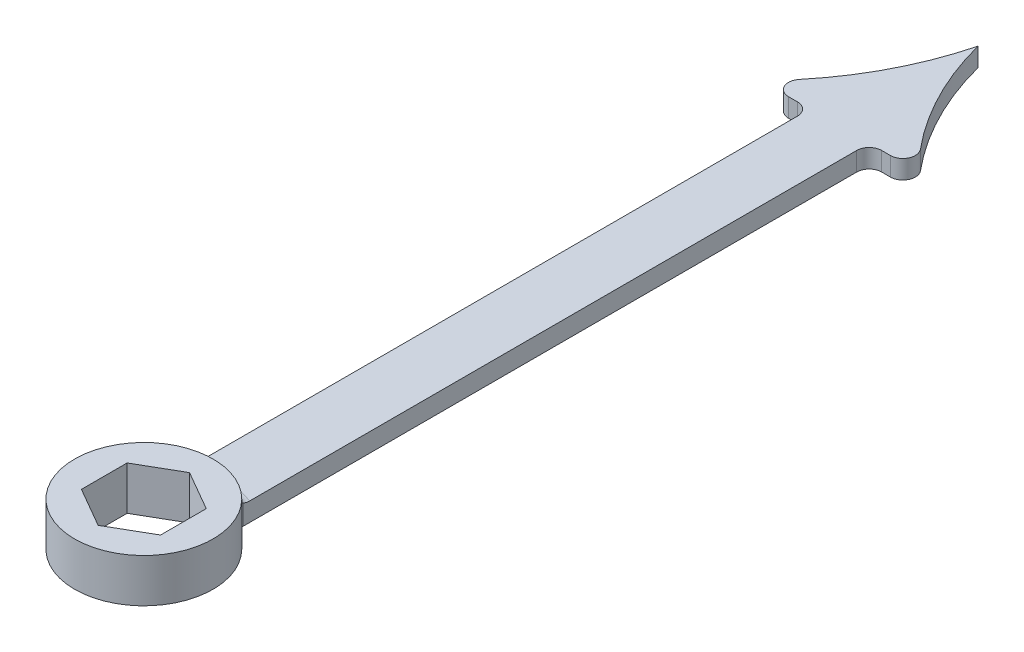
SolidWorks part; units mm, degrees
ref_plane "Front Plane" through (0, 0, 0) normal (0, 0, 1) x (1, 0, 0)
ref_plane "Top Plane" through (0, 0, 0) normal (0, 1, 0) x (1, 0, 0)
ref_plane "Right Plane" through (0, 0, 0) normal (1, 0, 0) x (0, 0, -1)
sketch "Sketch1" plane through (0, 0, 0) normal (0, 1, 0) x (1, 0, 0)
  line L1 (6.35, 3.6662) -> (0, 7.3323)
  line L2 (0, 7.3323) -> (-6.35, 3.6662)
  line L3 (-6.35, 3.6662) -> (-6.35, -3.6662)
  line L4 (-6.35, -3.6662) -> (0, -7.3323)
  line L5 (0, -7.3323) -> (6.35, -3.6662)
  line L6 (6.35, -3.6662) -> (6.35, 3.6662)
  circle A0 centre (0, 0) radius 6.35 construction
  circle A1 centre (0, 0) radius 11.1125
  dimension "D2" = 22.225
  dimension "D1" = 12.7
extrude "Boss-Extrude1" add sketch "Sketch1" along normal blind 7
sketch "Sketch2" plane through (0, 0, 0) normal (0, 1, 0) x (1, 0, 0)
  line L0 (-4.7625, 111.6402) -> (-12.7, 111.6402)
  line L1 (-4.7625, 111.6402) -> (4.7625, 111.6402) construction
  line L2 (-4.7625, 111.6402) -> (-4.7625, 10.0402)
  line L3 (-4.7625, 10.0402) -> (4.7625, 10.0402)
  line L4 (4.7625, 111.6402) -> (4.7625, 10.0402)
  line L5 (-12.7, 111.6402) -> (0, 124.3402) construction
  line L6 (0, 124.3402) -> (12.7, 111.6402) construction
  line L7 (12.7, 111.6402) -> (4.7625, 111.6402)
  line L8 (0, 133.8652) -> (0, 124.3402) construction
  circle A0 centre (0, 0) radius 11.1125 construction
  arc A1 (-12.7, 111.6402) -> (0, 133.8652) centre (-47.0958, 146.0361) ccw
  arc A2 (12.7, 111.6402) -> (0, 133.8652) centre (47.0958, 146.0361) cw
  point P11 (12.7, 111.6402)
  point P12 (0, 133.5515)
  dimension "D1" = 9.525
  dimension "D2" = 101.6
  dimension "D3" = 90
  dimension "D4" = 12.7
  dimension "D5" = 9.525
extrude "Boss-Extrude2" add sketch "Sketch2" along normal blind 3
fillet "Fillet1" radius 2 7 edges at (-12.7, 1.5, -111.6402) (12.7, 1.5, -111.6402) (4.7625, 1.5, -111.6402) (-4.7625, 1.5, -111.6402) (4.7625, 1.5, -10.0402) (0, 3, -11.1125) (-4.7625, 1.5, -10.0402)
